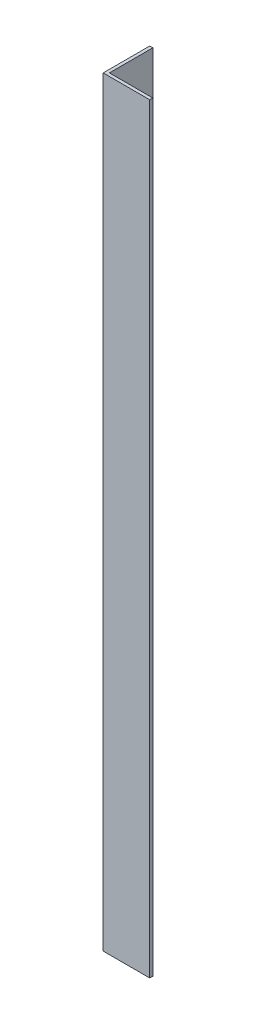
SolidWorks part; units mm, degrees
material "1060 Сплав"
ref_plane "Спереди" through (0, 0, 0) normal (0, 0, 1) x (1, 0, 0)
ref_plane "Сверху" through (0, 0, 0) normal (0, 1, 0) x (1, 0, 0)
ref_plane "Справа" through (0, 0, 0) normal (1, 0, 0) x (0, 0, -1)
sketch "Эскиз1" plane through (0, 0, 0) normal (0, 1, 0) x (1, 0, 0)
  line L0 (0, 0) -> (0, 15)
  line L1 (0, 15) -> (1, 15)
  line L2 (1, 15) -> (1, 1)
  line L3 (1, 1) -> (15, 1)
  line L4 (15, 1) -> (15, 0)
  line L5 (15, 0) -> (0, 0)
  dimension "D1" = 1
  dimension "D2" = 15
extrude "Бобышка-Вытянуть1" add sketch "Эскиз1" along normal blind 245
